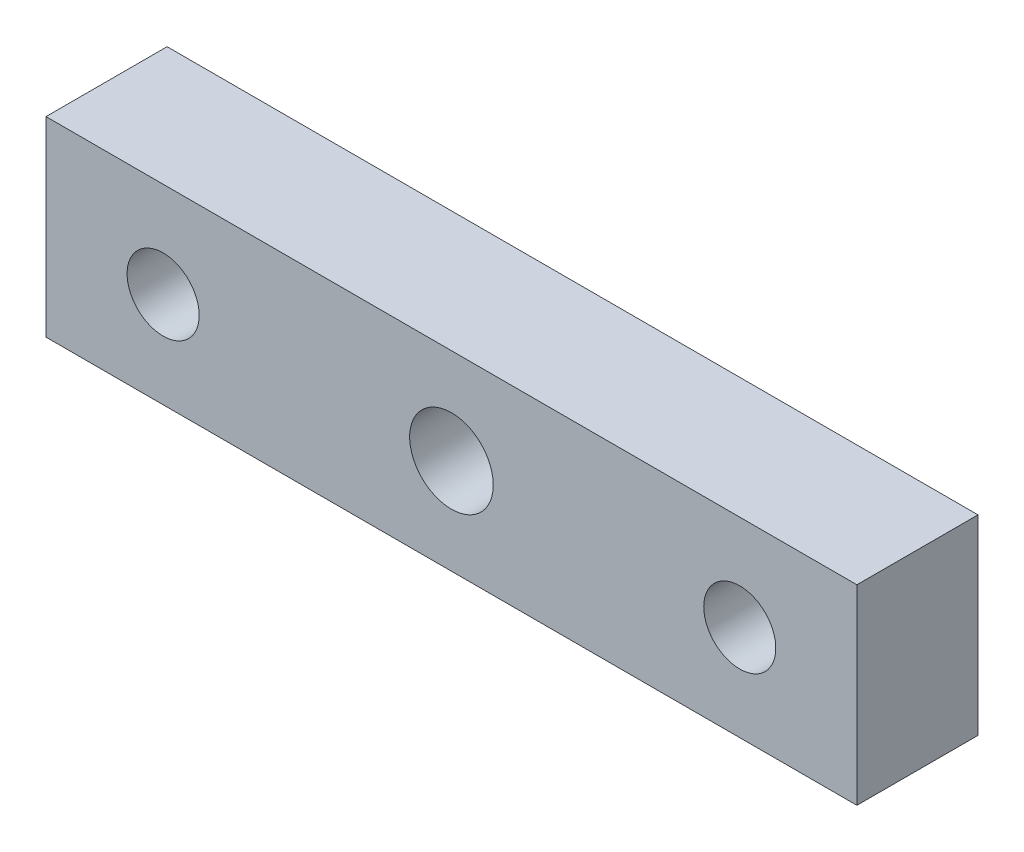
SolidWorks part; units mm, degrees
ref_plane "Front" through (0, 0, 0) normal (0, 0, 1) x (1, 0, 0)
ref_plane "Top" through (0, 0, 0) normal (0, 1, 0) x (1, 0, 0)
ref_plane "Right" through (0, 0, 0) normal (1, 0, 0) x (0, 0, -1)
sketch "Sketch1" plane through (0, 0, 0) normal (0, 0, 1) x (1, 0, 0)
  line L0 (-28.125, 0) -> (28.125, 0) construction
  line L1 (-28.125, -6.625) -> (28.125, -6.625)
  line L2 (-28.125, -6.625) -> (-28.125, 6.625)
  line L3 (-28.125, 6.625) -> (28.125, 6.625)
  line L4 (28.125, -6.625) -> (28.125, 6.625)
  line L5 (-28.125, -6.625) -> (28.125, 6.625) construction
  line L6 (-28.125, 6.625) -> (28.125, -6.625) construction
  line L7 (0, 6.625) -> (0, -6.625) construction
  circle A0 centre (0, 0) radius 2.9
  circle A1 centre (-20, 0) radius 2.5
  circle A2 centre (20, 0) radius 2.5
  point P0 (0, 0)
  dimension "D3" = 5.8
  dimension "D4" = 5
  dimension "D5" = 20
  dimension "D1" = 56.25
  dimension "D2" = 13.25
extrude "Boss-Extrude1" add sketch "Sketch1" along normal blind 8.4
